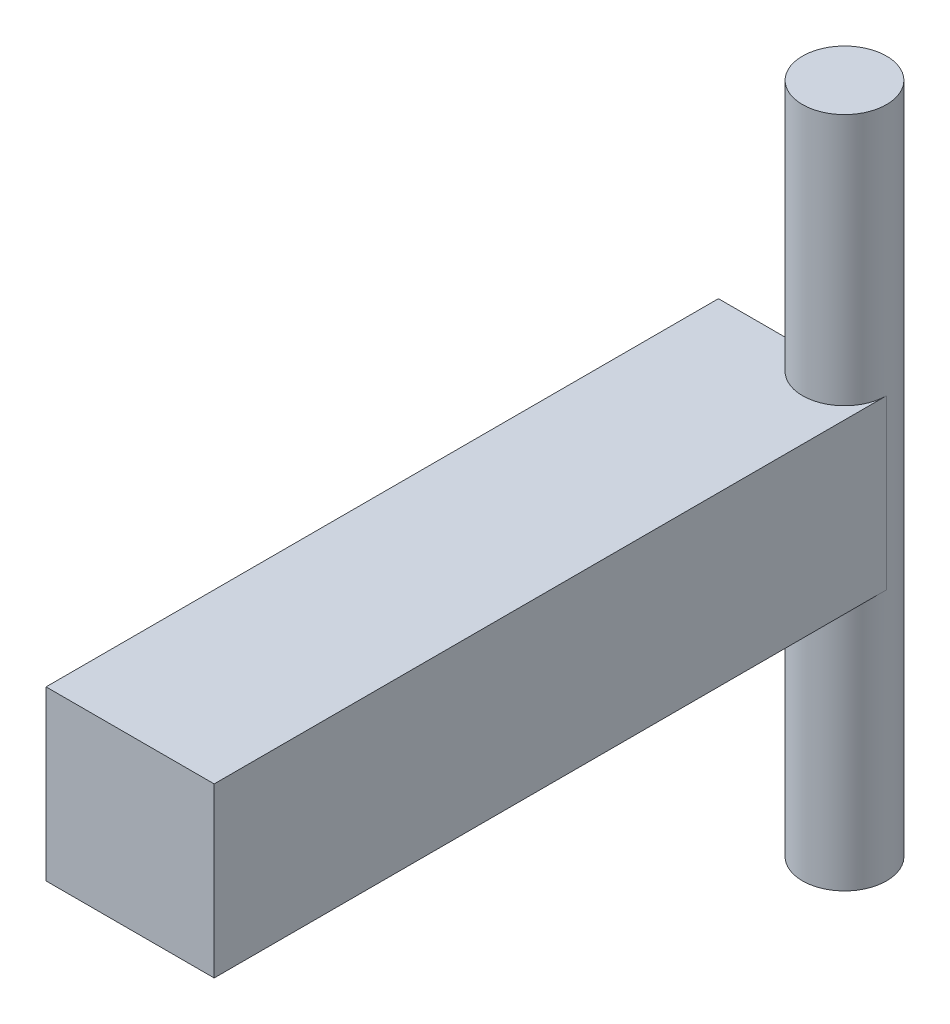
SolidWorks part; units mm, degrees
ref_plane "Front" through (0, 0, 0) normal (0, 0, 1) x (1, 0, 0)
ref_plane "Top" through (0, 0, 0) normal (0, 1, 0) x (1, 0, 0)
ref_plane "Right" through (0, 0, 0) normal (1, 0, 0) x (0, 0, -1)
sketch "草图1" plane through (0, 0, 0) normal (0, 0, 1) x (1, 0, 0)
  line L1 (-2, 2) -> (2, 2)
  line L2 (-2, 2) -> (-2, -2)
  line L3 (-2, -2) -> (2, -2)
  line L4 (2, 2) -> (2, -2)
  dimension "D1" = 4
  dimension "D2" = 4
  dimension "D3" = 2
  dimension "D4" = 2
extrude "凸台-拉伸1" add sketch "草图1" along normal blind 16
sketch "草图3" plane through (0, 0, 0) normal (0, 1, 0) x (1, 0, 0)
  line L0 (2, 0) -> (-2, 0) construction
  circle A0 centre (1, 0) radius 1
extrude "凸台-拉伸2" add sketch "草图3" along normal mid plane 16
